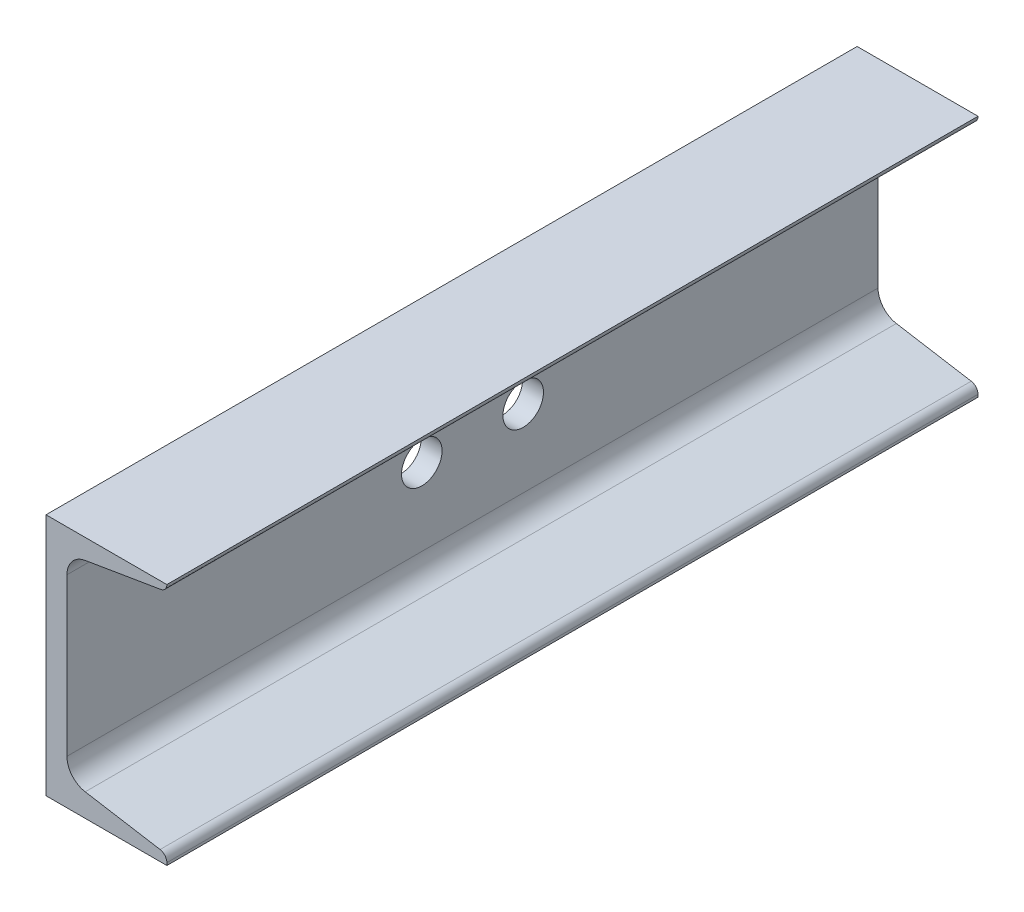
SolidWorks part; units mm, degrees
ref_plane "Front" through (0, 0, 0) normal (0, 0, 1) x (1, 0, 0)
ref_plane "Top" through (0, 0, 0) normal (0, 1, 0) x (1, 0, 0)
ref_plane "Right" through (0, 0, 0) normal (1, 0, 0) x (0, 0, -1)
sketch "Sketch1" plane through (0, 0, 0) normal (0, 0, 1) x (1, 0, 0)
  line L0 (37.846, -38.1) -> (0, -38.1)
  line L1 (0, -38.1) -> (0, 38.1)
  line L2 (0, 38.1) -> (37.846, 38.1)
  line L3 (37.846, 38.1) -> (37.846, 38.0954)
  line L4 (37.846, -38.1) -> (37.846, -37.3185)
  line L5 (6.5532, 25.1016) -> (6.5532, -24.1259)
  line L6 (12.2793, 31.8656) -> (35.9373, 35.8246)
  line L7 (12.2793, -30.8899) -> (35.7252, -34.8134)
  line L8 (37.846, 38.0954) -> (37.846, 38.0792)
  arc A0 (6.5532, -24.1259) -> (12.2793, -30.8899) centre (13.4112, -24.1259) ccw
  arc A1 (12.2793, 31.8656) -> (6.5532, 25.1016) centre (13.4112, 25.1016) ccw
  arc A2 (35.7252, -34.8134) -> (37.846, -37.3185) centre (35.306, -37.3185) cw
  arc A3 (35.9373, 35.8246) -> (37.846, 38.0792) centre (35.56, 38.0792) ccw
  dimension "D9" = 2.54
  dimension "D10" = 6.858
  dimension "D4" = 6.5532
  dimension "D5" = 9.5
  dimension "D8" = 6.858
  dimension "D11" = 2.286
  dimension "D1" = 76.2
  dimension "D2" = 37.846
  dimension "D3" = 37.846
  dimension "D6" = 38.1
  dimension "D7" = 9.5
extrude "Boss-Extrude1" add sketch "Sketch1" along normal mid plane 254
sketch "Sketch3" plane through (0, 0, 0) normal (-1, 0, 0) x (0, 0, 1)
  circle A0 centre (-15.875, 0) radius 6.35
  circle A1 centre (15.875, 0) radius 6.35
  dimension "D1" = 12.7
  dimension "D2" = 12.7
  dimension "D3" = 15.875
  dimension "D4" = 31.75
extrude "Cut-Extrude1" cut sketch "Sketch3" against normal up to next
